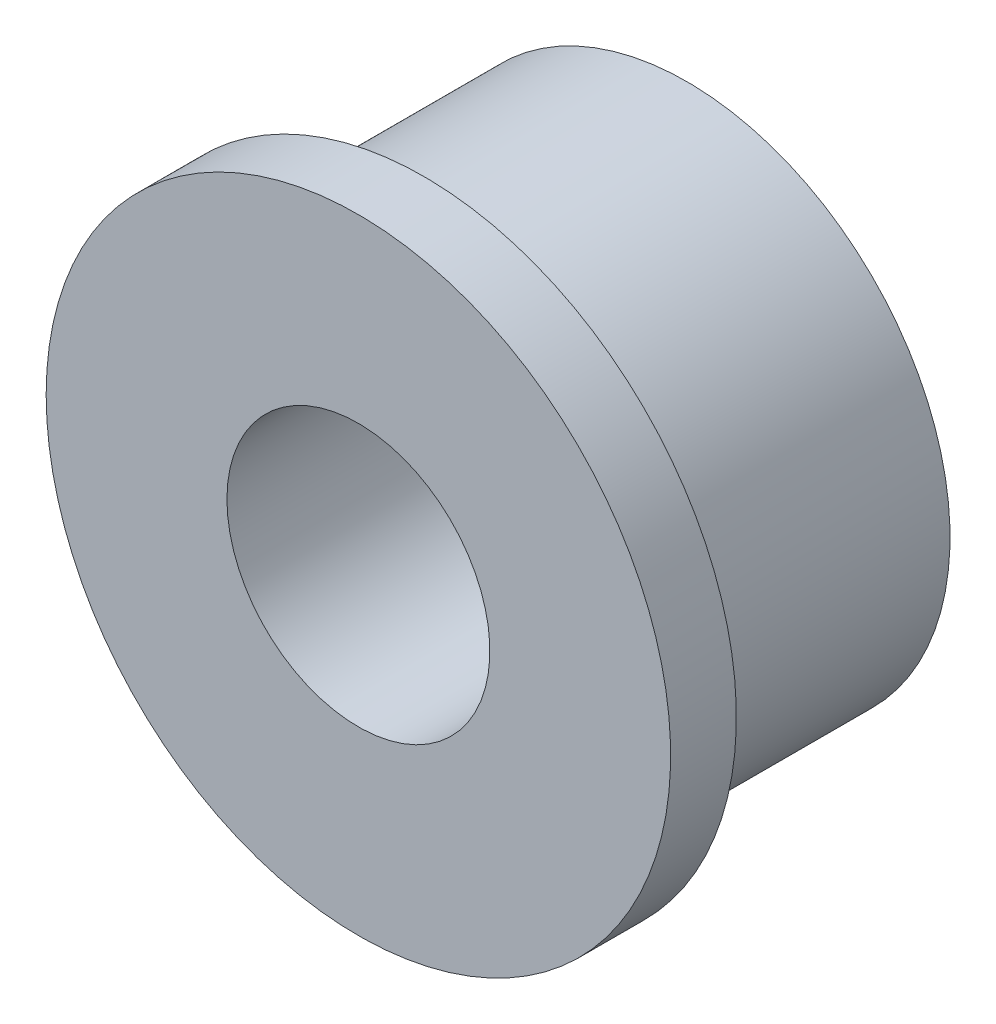
SolidWorks part; units mm, degrees
ref_plane "Спереди" through (0, 0, 0) normal (0, 0, 1) x (1, 0, 0)
ref_plane "Сверху" through (0, 0, 0) normal (0, 1, 0) x (1, 0, 0)
ref_plane "Справа" through (0, 0, 0) normal (1, 0, 0) x (0, 0, -1)
sketch "Эскиз1" plane through (0, 0, 0) normal (0, 1, 0) x (1, 0, 0)
  line L0 (-4, 5.5271) -> (-4, -1.7241) construction
  line L1 (0, 0) -> (5.5, 0)
  line L2 (0, 0) -> (0, 2)
  line L3 (0, 2) -> (5.5, 2)
  line L4 (5.5, 0) -> (5.5, 2)
  line L5 (4, 2) -> (4, 10)
  line L6 (0, 2) -> (0, 7.1992)
  line L7 (0, 7.1992) -> (4, 10)
  dimension "D1" = 2
  dimension "D2" = 5.5
  dimension "D3" = 4
  dimension "D4" = 7.2512
  dimension "D5" = 8
  dimension "D6" = 8
  dimension "D7" = 55
revolve "Повернуть1" add sketch "Эскиз1" angle 360 about L0
